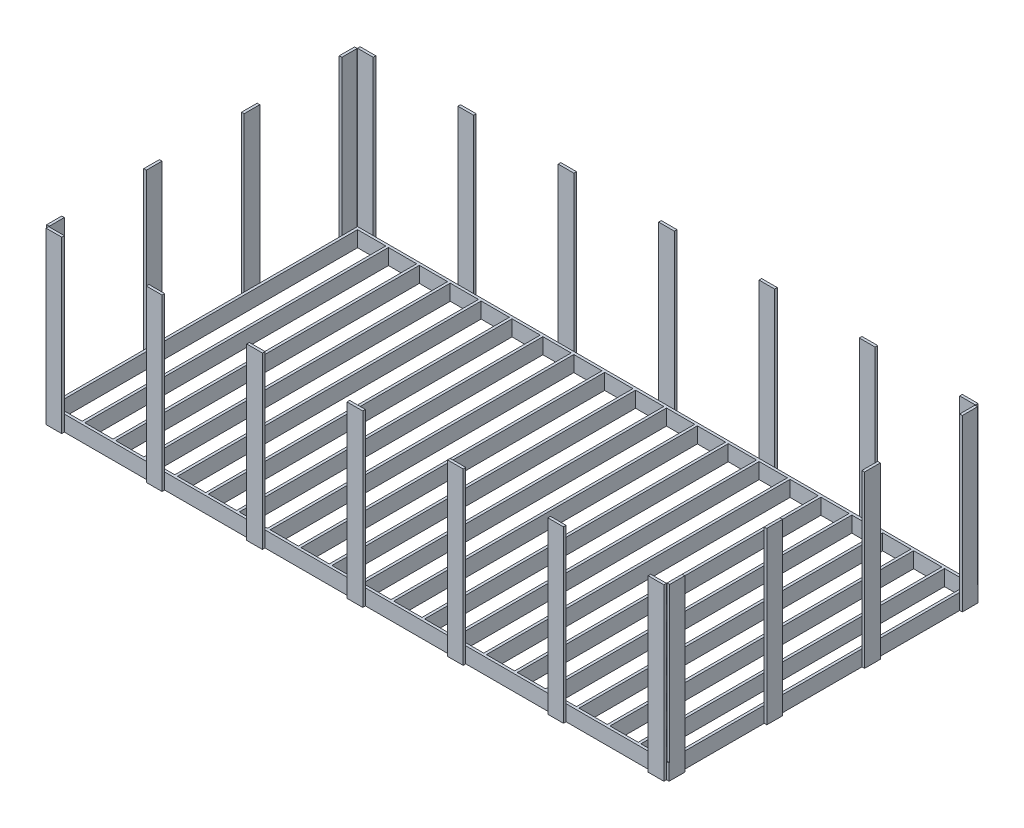
SolidWorks part; units mm, degrees
ref_plane "前视基准面" through (0, 0, 0) normal (0, 0, 1) x (1, 0, 0)
ref_plane "上视基准面" through (0, 0, 0) normal (0, 1, 0) x (1, 0, 0)
ref_plane "右视基准面" through (0, 0, 0) normal (1, 0, 0) x (0, 0, -1)
sketch "草图2" plane through (0, 0, 0) normal (0, 1, 0) x (1, 0, 0)
  line L0 (325.6, 2974.4) -> (325.6, 25.6)
  line L1 (0, 0) -> (6000, 0)
  line L2 (0, 0) -> (0, 3000)
  line L3 (0, 3000) -> (6000, 3000)
  line L4 (6000, 0) -> (6000, 3000)
  line L5 (25.6, 2974.4) -> (300, 2974.4)
  line L6 (25.6, 2974.4) -> (25.6, 25.6)
  line L7 (25.6, 25.6) -> (300, 25.6)
  line L8 (300, 2974.4) -> (300, 25.6)
  line L9 (325.6, 2974.4) -> (600, 2974.4)
  line L10 (600, 2974.4) -> (600, 25.6)
  line L11 (325.6, 25.6) -> (600, 25.6)
  line L12 (925.6, 2974.4) -> (925.6, 25.6)
  line L13 (925.6, 25.6) -> (1200, 25.6)
  line L14 (1200, 2974.4) -> (1200, 25.6)
  line L15 (925.6, 2974.4) -> (1200, 2974.4)
  line L16 (625.6, 2974.4) -> (625.6, 25.6)
  line L17 (625.6, 2974.4) -> (900, 2974.4)
  line L18 (900, 2974.4) -> (900, 25.6)
  line L19 (625.6, 25.6) -> (900, 25.6)
  line L20 (2125.6, 2974.4) -> (2125.6, 25.6)
  line L21 (2125.6, 25.6) -> (2400, 25.6)
  line L22 (2400, 2974.4) -> (2400, 25.6)
  line L23 (2125.6, 2974.4) -> (2400, 2974.4)
  line L24 (1825.6, 2974.4) -> (1825.6, 25.6)
  line L25 (1825.6, 25.6) -> (2100, 25.6)
  line L26 (2100, 2974.4) -> (2100, 25.6)
  line L27 (1825.6, 2974.4) -> (2100, 2974.4)
  line L28 (1525.6, 2974.4) -> (1525.6, 25.6)
  line L29 (1525.6, 25.6) -> (1800, 25.6)
  line L30 (1800, 2974.4) -> (1800, 25.6)
  line L31 (1525.6, 2974.4) -> (1800, 2974.4)
  line L32 (1225.6, 2974.4) -> (1225.6, 25.6)
  line L33 (1225.6, 2974.4) -> (1500, 2974.4)
  line L34 (1500, 2974.4) -> (1500, 25.6)
  line L35 (1225.6, 25.6) -> (1500, 25.6)
  line L36 (4525.6, 2974.4) -> (4525.6, 25.6)
  line L37 (4525.6, 25.6) -> (4800, 25.6)
  line L38 (4800, 2974.4) -> (4800, 25.6)
  line L39 (4525.6, 2974.4) -> (4800, 2974.4)
  line L40 (4225.6, 2974.4) -> (4225.6, 25.6)
  line L41 (4225.6, 25.6) -> (4500, 25.6)
  line L42 (4500, 2974.4) -> (4500, 25.6)
  line L43 (4225.6, 2974.4) -> (4500, 2974.4)
  line L44 (3925.6, 2974.4) -> (3925.6, 25.6)
  line L45 (3925.6, 25.6) -> (4200, 25.6)
  line L46 (4200, 2974.4) -> (4200, 25.6)
  line L47 (3925.6, 2974.4) -> (4200, 2974.4)
  line L48 (3625.6, 2974.4) -> (3625.6, 25.6)
  line L49 (3625.6, 25.6) -> (3900, 25.6)
  line L50 (3900, 2974.4) -> (3900, 25.6)
  line L51 (3625.6, 2974.4) -> (3900, 2974.4)
  line L52 (3325.6, 2974.4) -> (3325.6, 25.6)
  line L53 (3325.6, 25.6) -> (3600, 25.6)
  line L54 (3600, 2974.4) -> (3600, 25.6)
  line L55 (3325.6, 2974.4) -> (3600, 2974.4)
  line L56 (3025.6, 2974.4) -> (3025.6, 25.6)
  line L57 (3025.6, 25.6) -> (3300, 25.6)
  line L58 (3300, 2974.4) -> (3300, 25.6)
  line L59 (3025.6, 2974.4) -> (3300, 2974.4)
  line L60 (2725.6, 2974.4) -> (2725.6, 25.6)
  line L61 (2725.6, 25.6) -> (3000, 25.6)
  line L62 (3000, 2974.4) -> (3000, 25.6)
  line L63 (2725.6, 2974.4) -> (3000, 2974.4)
  line L64 (2425.6, 2974.4) -> (2425.6, 25.6)
  line L65 (2425.6, 2974.4) -> (2700, 2974.4)
  line L66 (2700, 2974.4) -> (2700, 25.6)
  line L67 (2425.6, 25.6) -> (2700, 25.6)
  line L68 (5425.6, 2974.4) -> (5425.6, 25.6)
  line L69 (5425.6, 25.6) -> (5700, 25.6)
  line L70 (5700, 2974.4) -> (5700, 25.6)
  line L71 (5425.6, 2974.4) -> (5700, 2974.4)
  line L72 (5125.6, 2974.4) -> (5125.6, 25.6)
  line L73 (5125.6, 25.6) -> (5400, 25.6)
  line L74 (5400, 2974.4) -> (5400, 25.6)
  line L75 (5125.6, 2974.4) -> (5400, 2974.4)
  line L76 (4825.6, 2974.4) -> (4825.6, 25.6)
  line L77 (4825.6, 25.6) -> (5100, 25.6)
  line L78 (5100, 2974.4) -> (5100, 25.6)
  line L79 (4825.6, 2974.4) -> (5100, 2974.4)
  line L81 (5725.6, 2974.4) -> (5974.4, 2974.4)
  line L82 (5725.6, 2974.4) -> (5725.6, 25.6)
  line L83 (5725.6, 25.6) -> (5974.4, 25.6)
  line L84 (5974.4, 2974.4) -> (5974.4, 25.6)
  dimension "D1" = 6000
  dimension "D2" = 3000
  dimension "D3" = 25.6
  dimension "D4" = 25.6
  dimension "D5" = 25.6
  dimension "D6" = 274.4
  dimension "D12" = 25.6
  dimension "D13" = 25.6
  dimension "D14" = 25.6
  dimension "D15" = 25.6
  dimension "D16" = 25.6
  dimension "D17" = 25.6
  dimension "D18" = 25.6
  dimension "D19" = 25.6
  dimension "D20" = 25.6
  dimension "D7" = 2
  dimension "D8" = 2
  dimension "D9" = 2
  dimension "D10" = 2
  dimension "D11" = 2
extrude "凸台-拉伸1" add sketch "草图2" along normal blind 152.4
sketch "草图5" plane through (0, 0, 0) normal (0, -1, 0) x (-1, 0, 0)
  line L0 (-974.6, 2999.8) -> (-1127, 2999.8)
  line L1 (0, 3000) -> (-152.4, 3000)
  line L2 (0, 3000) -> (0, 3025.4)
  line L3 (0, 3025.4) -> (-152.4, 3025.4)
  line L4 (-152.4, 3000) -> (-152.4, 3025.4)
  line L5 (-974.6, 2999.8) -> (-974.6, 3025.2)
  line L6 (-974.6, 3025.2) -> (-1127, 3025.2)
  line L7 (-1127, 2999.8) -> (-1127, 3025.2)
  line L8 (-1949.2, 2999.8) -> (-2101.6, 2999.8)
  line L9 (-1949.2, 2999.8) -> (-1949.2, 3025.2)
  line L10 (-1949.2, 3025.2) -> (-2101.6, 3025.2)
  line L11 (-2101.6, 2999.8) -> (-2101.6, 3025.2)
  line L12 (-2923.8, 3000) -> (-3076.2, 3000)
  line L13 (-2923.8, 3000) -> (-2923.8, 3025.4)
  line L14 (-2923.8, 3025.4) -> (-3076.2, 3025.4)
  line L15 (-3076.2, 3000) -> (-3076.2, 3025.4)
  line L16 (-3898.4, 3000) -> (-4050.8, 3000)
  line L17 (-3898.4, 3000) -> (-3898.4, 3025.4)
  line L18 (-3898.4, 3025.4) -> (-4050.8, 3025.4)
  line L19 (-4050.8, 3000) -> (-4050.8, 3025.4)
  line L20 (-4873, 3000) -> (-5025.4, 3000)
  line L21 (-4873, 3000) -> (-4873, 3025.4)
  line L22 (-4873, 3025.4) -> (-5025.4, 3025.4)
  line L23 (-5025.4, 3000) -> (-5025.4, 3025.4)
  line L24 (-5847.6, 3000) -> (-6000, 3000)
  line L25 (-5847.6, 3000) -> (-5847.6, 3025.4)
  line L26 (-5847.6, 3025.4) -> (-6000, 3025.4)
  line L27 (-6000, 3000) -> (-6000, 3025.4)
  line L28 (-900, 2974.4) -> (-625.6, 2974.4) construction
  line L29 (-2100, 2974.4) -> (-1825.6, 2974.4) construction
  line L30 (-6000, 3000) -> (0, 3000) construction
  line L31 (-6000, 0) -> (-6000, 3000) construction
  line L32 (0, 1500) -> (-5974.4, 1500) construction
  line L33 (0, 3000) -> (0, 0) construction
  line L34 (-5974.4, 25.6) -> (-5974.4, 2974.4) construction
  line L35 (-6000, 0) -> (-6000, -25.4)
  line L36 (-5847.6, -25.4) -> (-6000, -25.4)
  line L37 (-5847.6, 0) -> (-5847.6, -25.4)
  line L38 (-5847.6, 0) -> (-6000, 0)
  line L39 (-5025.4, 0) -> (-5025.4, -25.4)
  line L40 (-4873, -25.4) -> (-5025.4, -25.4)
  line L41 (-4873, 0) -> (-4873, -25.4)
  line L42 (-4873, 0) -> (-5025.4, 0)
  line L43 (-4050.8, 0) -> (-4050.8, -25.4)
  line L44 (-3898.4, -25.4) -> (-4050.8, -25.4)
  line L45 (-3898.4, 0) -> (-3898.4, -25.4)
  line L46 (-3898.4, 0) -> (-4050.8, 0)
  line L47 (-3076.2, 0) -> (-3076.2, -25.4)
  line L48 (-2923.8, -25.4) -> (-3076.2, -25.4)
  line L49 (-2923.8, 0) -> (-2923.8, -25.4)
  line L50 (-2923.8, 0) -> (-3076.2, 0)
  line L51 (-2101.6, 0.2) -> (-2101.6, -25.2)
  line L52 (-1949.2, -25.2) -> (-2101.6, -25.2)
  line L53 (-1949.2, 0.2) -> (-1949.2, -25.2)
  line L54 (-1949.2, 0.2) -> (-2101.6, 0.2)
  line L55 (-1127, 0.2) -> (-1127, -25.2)
  line L56 (-974.6, -25.2) -> (-1127, -25.2)
  line L57 (-974.6, 0.2) -> (-974.6, -25.2)
  line L58 (-152.4, 0) -> (-152.4, -25.4)
  line L59 (0, -25.4) -> (-152.4, -25.4)
  line L60 (0, 0) -> (0, -25.4)
  line L61 (0, 0) -> (-152.4, 0)
  line L62 (-974.6, 0.2) -> (-1127, 0.2)
  point P31 (-974.6, 3012.5)
  point P36 (-4873, 3012.7)
  dimension "D1" = 25.4
  dimension "D2" = 152.4
  dimension "D3" = 152.4
  dimension "D4" = 152.4
  dimension "D5" = 152.4
  dimension "D6" = 152.4
  dimension "D7" = 152.4
  dimension "D8" = 152.4
  dimension "D9" = 25.4
  dimension "D10" = 25.4
  dimension "D11" = 974.6
  dimension "D12" = 25.4
  dimension "D13" = 25.4
  dimension "D14" = 974.6
  dimension "D15" = 25.4
  dimension "D16" = 25.4
  dimension "D17" = 974.6
  dimension "D18" = 25.4
  dimension "D19" = 25.4
  dimension "D20" = 974.6
  dimension "D21" = 25.4
  dimension "D22" = 25.4
  dimension "D23" = 974.6
  dimension "D24" = 25.4
  dimension "D25" = 25.4
  dimension "D26" = 152.4
extrude "凸台-拉伸2" add sketch "草图5" against normal blind 1652.4
sketch "草图6" plane through (0, 0, 0) normal (0, -1, 0) x (1, 0, 0)
  line L0 (152.4, 25.4) -> (0, 25.4) construction
  line L1 (0, -3025.4) -> (0, 25.4) construction
  line L3 (0, 0) -> (-25.4, 0)
  line L4 (0, 0) -> (0, -152.4)
  line L5 (0, -152.4) -> (-25.4, -152.4)
  line L6 (-25.4, 0) -> (-25.4, -152.4)
  line L7 (0, -949.2) -> (-25.4, -949.2)
  line L8 (0, -949.2) -> (0, -1101.6)
  line L9 (0, -1101.6) -> (-25.4, -1101.6)
  line L10 (-25.4, -949.2) -> (-25.4, -1101.6)
  line L11 (0, -1898.4) -> (-25.4, -1898.4)
  line L12 (0, -1898.4) -> (0, -2050.8)
  line L13 (0, -2050.8) -> (-25.4, -2050.8)
  line L14 (-25.4, -1898.4) -> (-25.4, -2050.8)
  line L15 (0, -2847.6) -> (-25.4, -2847.6)
  line L16 (0, -2847.6) -> (0, -3000)
  line L17 (0, -3000) -> (-25.4, -3000)
  line L18 (-25.4, -2847.6) -> (-25.4, -3000)
  line L19 (3000, 25.4) -> (3000, -3025.4) construction
  line L20 (3076.2, 25.4) -> (2923.8, 25.4) construction
  line L21 (2923.8, -3025.4) -> (3076.2, -3025.4) construction
  line L23 (6025.4, -2847.6) -> (6025.4, -3000)
  line L24 (6000, -3000) -> (6025.4, -3000)
  line L25 (6000, -2847.6) -> (6000, -3000)
  line L26 (6000, -2847.6) -> (6025.4, -2847.6)
  line L27 (6025.4, -1898.4) -> (6025.4, -2050.8)
  line L28 (6000, -2050.8) -> (6025.4, -2050.8)
  line L29 (6000, -1898.4) -> (6000, -2050.8)
  line L30 (6000, -1898.4) -> (6025.4, -1898.4)
  line L31 (6025.4, -949.2) -> (6025.4, -1101.6)
  line L32 (6000, -1101.6) -> (6025.4, -1101.6)
  line L33 (6000, -949.2) -> (6000, -1101.6)
  line L34 (6000, -949.2) -> (6025.4, -949.2)
  line L35 (6025.4, 0) -> (6025.4, -152.4)
  line L36 (6000, -152.4) -> (6025.4, -152.4)
  line L37 (6000, 0) -> (6000, -152.4)
  line L38 (6000, 0) -> (6025.4, 0)
  dimension "D1" = 152.4
  dimension "D2" = 25.4
  dimension "D3" = 152.4
  dimension "D4" = 25.4
  dimension "D5" = 25.4
  dimension "D6" = 949.2
  dimension "D7" = 25.4
  dimension "D8" = 152.4
  dimension "D9" = 25.4
  dimension "D10" = 949.2
  dimension "D11" = 949.2
  dimension "D12" = 25.4
  dimension "D13" = 25.4
  dimension "D14" = 152.4
  dimension "D15" = 25.4
extrude "凸台-拉伸5" add sketch "草图6" against normal blind 152.4 separate body
sketch "草图7" plane through (0, 152.4, 0) normal (0, 1, 0) x (1, 0, 0)
  line L0 (0, 3000) -> (0, 0) construction
  line L1 (-25.4, 2847.6) -> (0, 2847.6)
  line L2 (-25.4, 2847.6) -> (-25.4, 2996.5574)
  line L3 (-25.4, 2996.5574) -> (0, 2996.5574)
  line L4 (0, 2847.6) -> (0, 2996.5574)
  line L5 (-25.4, 0) -> (-25.4, 152.4) construction
  line L6 (-25.4, 2050.8) -> (0, 2050.8)
  line L7 (-25.4, 2050.8) -> (-25.4, 1898.4)
  line L8 (-25.4, 1898.4) -> (0, 1898.4)
  line L9 (0, 2050.8) -> (0, 1898.4)
  line L10 (-25.4, 1101.6) -> (0, 1101.6)
  line L11 (-25.4, 1101.6) -> (-25.4, 949.2)
  line L12 (-25.4, 949.2) -> (0, 949.2)
  line L13 (0, 1101.6) -> (0, 949.2)
  line L14 (-25.4, 152.4) -> (0, 152.4)
  line L15 (-25.4, 152.4) -> (-25.4, 6.2486)
  line L16 (-25.4, 6.2486) -> (0, 6.2486)
  line L17 (0, 152.4) -> (0, 6.2486)
  line L18 (6000, 0) -> (6000, 3000) construction
  line L19 (6025.4, 2847.6) -> (6000, 2847.6)
  line L20 (6025.4, 2847.6) -> (6025.4, 2996.5574)
  line L21 (6025.4, 2996.5574) -> (6000, 2996.5574)
  line L22 (6000, 2847.6) -> (6000, 2996.5574)
  line L23 (6025.4, 2050.8) -> (6025.4, 1898.4) construction
  line L24 (6025.4, 2050.8) -> (6000, 2050.8)
  line L25 (6025.4, 2050.8) -> (6025.4, 1898.4)
  line L26 (6025.4, 1898.4) -> (6000, 1898.4)
  line L27 (6000, 2050.8) -> (6000, 1898.4)
  line L29 (6025.4, 1101.6) -> (6000, 1101.6)
  line L30 (6025.4, 1101.6) -> (6025.4, 949.2)
  line L31 (6025.4, 949.2) -> (6000, 949.2)
  line L32 (6000, 1101.6) -> (6000, 949.2)
  line L33 (6025.4, 152.4) -> (6000, 152.4)
  line L34 (6025.4, 152.4) -> (6025.4, 6.2486)
  line L35 (6025.4, 6.2486) -> (6000, 6.2486)
  line L36 (6000, 152.4) -> (6000, 6.2486)
extrude "凸台-拉伸6" add sketch "草图7" along normal blind 1500
